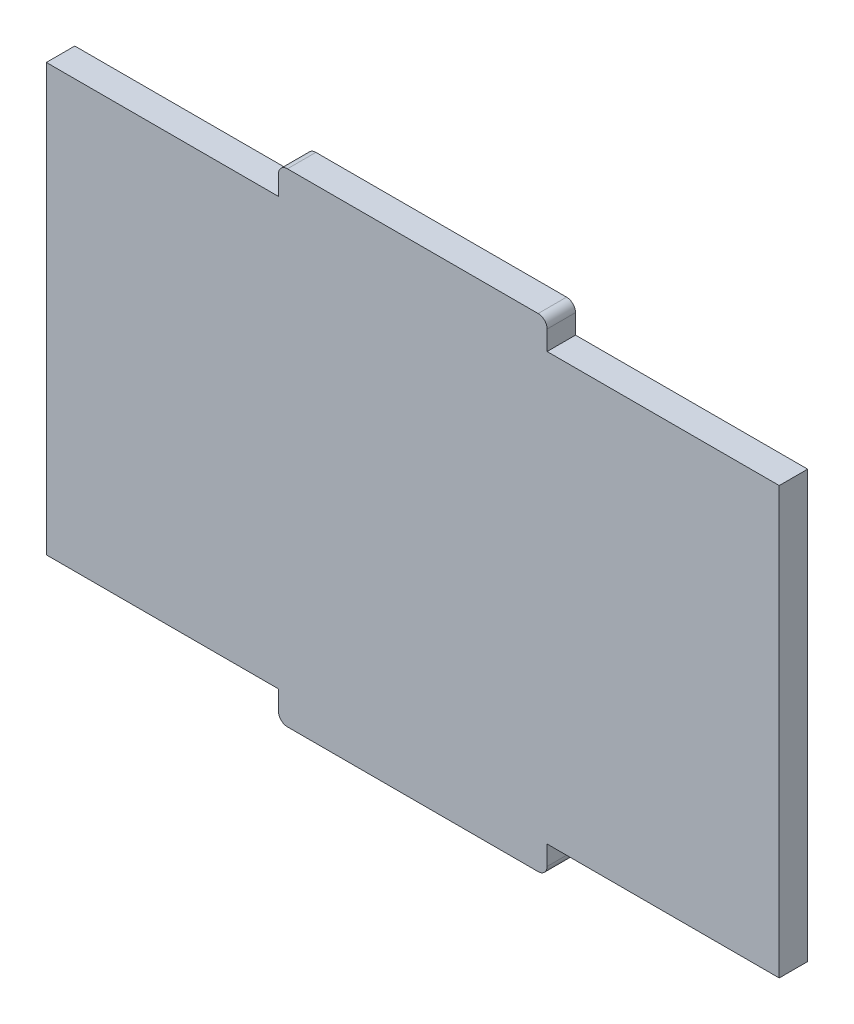
SolidWorks part; units mm, degrees
ref_plane "Front Plane" through (0, 0, 0) normal (0, 0, 1) x (1, 0, 0)
ref_plane "Top Plane" through (0, 0, 0) normal (0, 1, 0) x (1, 0, 0)
ref_plane "Right Plane" through (0, 0, 0) normal (1, 0, 0) x (0, 0, -1)
sketch "Sketch1" plane through (0, 0, 0) normal (0, 0, 1) x (1, 0, 0)
  line L0 (-13.2355, 23.815) -> (13.2355, 23.815) construction
  line L1 (-40.925, -23.815) -> (-15, -23.815)
  line L2 (-40.925, -23.815) -> (-40.925, 23.815)
  line L3 (-40.925, 23.815) -> (-15, 23.815)
  line L4 (40.925, -23.815) -> (40.925, 23.815)
  line L5 (-40.925, -23.815) -> (40.925, 23.815) construction
  line L6 (-40.925, 23.815) -> (40.925, -23.815) construction
  line L7 (-15, -26.99) -> (15, -26.99)
  line L8 (-15, -26.99) -> (-15, -23.815)
  line L9 (-15, 26.99) -> (15, 26.99)
  line L10 (15, -26.99) -> (15, -23.815)
  line L11 (-15, -26.99) -> (15, 26.99) construction
  line L12 (-15, 26.99) -> (15, -26.99) construction
  line L13 (15, 23.815) -> (40.925, 23.815)
  line L14 (-15, 23.815) -> (-13.2355, 23.815) construction
  line L15 (13.2355, 23.815) -> (15, 23.815) construction
  line L16 (15, 8.7288) -> (15, 23.815) construction
  line L17 (15, 23.815) -> (15, 26.99)
  line L18 (15, -8.7288) -> (15, 8.7288) construction
  line L19 (15, -23.815) -> (15, -8.7288) construction
  line L20 (-15, -23.815) -> (-15, -8.7288) construction
  line L21 (-15, 23.815) -> (-15, 26.99)
  line L22 (-15, -8.7288) -> (-15, 8.7288) construction
  line L23 (-15, 8.7288) -> (-15, 23.815) construction
  line L24 (-15, -23.815) -> (-13.2355, -23.815) construction
  line L25 (15, -23.815) -> (40.925, -23.815)
  line L26 (-13.2355, -23.815) -> (13.2355, -23.815) construction
  line L27 (13.2355, -23.815) -> (15, -23.815) construction
  point P0 (0, 0)
  point P6 (0, 0)
  point P23 (15, -25.4025)
  dimension "D1" = 81.85
  dimension "D2" = 47.63
  dimension "D3" = 53.98
  dimension "D4" = 30
extrude "Boss-Extrude1" add sketch "Sketch1" along normal blind 3.175 contours L3 L21 L9 L17 L13 L4 L25 L10 L7 L8 L1 L2
fillet "Fillet1" radius 1 4 edges at (15, -26.99, 1.5875) (-15, -26.99, 1.5875) (-15, 26.99, 1.5875) (15, 26.99, 1.5875)
